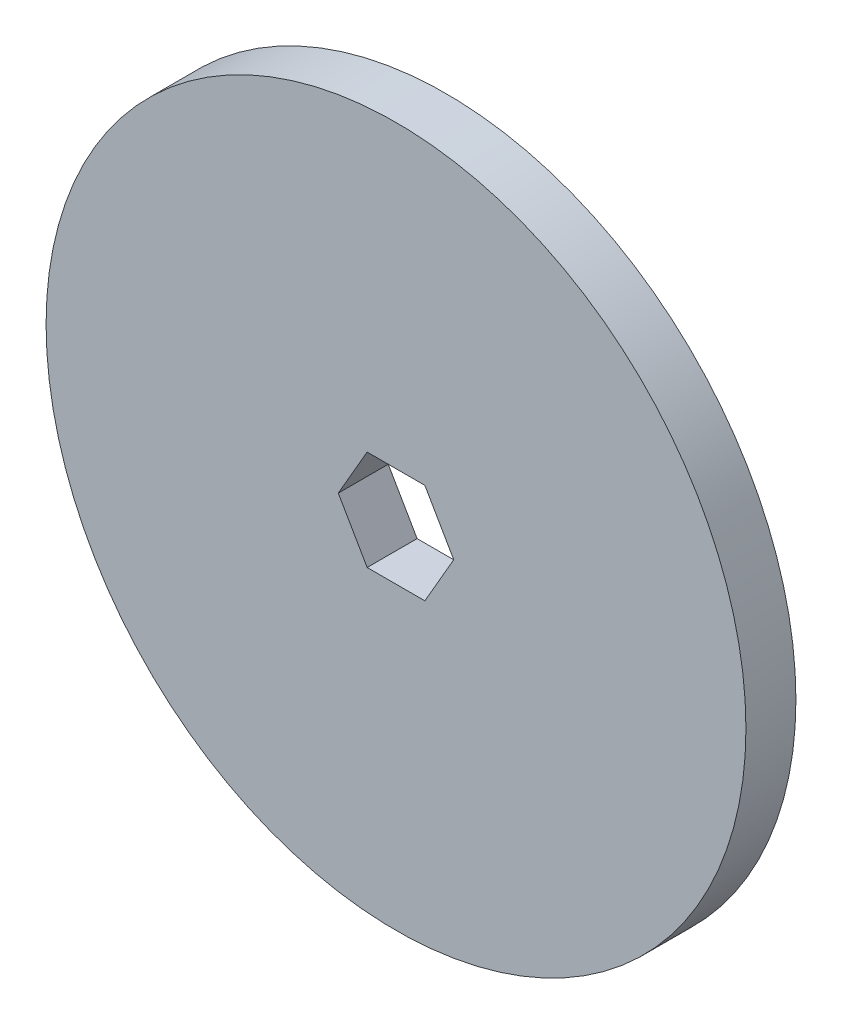
SolidWorks part; units mm, degrees
ref_plane "Front Plane" through (0, 0, 0) normal (0, 0, 1) x (1, 0, 0)
ref_plane "Top Plane" through (0, 0, 0) normal (0, 1, 0) x (1, 0, 0)
ref_plane "Right Plane" through (0, 0, 0) normal (1, 0, 0) x (0, 0, -1)
sketch "Sketch1" plane through (0, 0, 0) normal (0, 0, 1) x (1, 0, 0)
  circle A0 centre (0, 0) radius 44.45
  dimension "D1" = 88.9
extrude "Boss-Extrude1" add sketch "Sketch1" along normal mid plane 6.35
sketch "Sketch2" plane through (0, 0, 0) normal (0, 0, 1) x (1, 0, 0)
  line L1 (7.3323, 0) -> (3.6662, 6.35)
  line L2 (3.6662, 6.35) -> (-3.6662, 6.35)
  line L3 (-3.6662, 6.35) -> (-7.3323, 0)
  line L4 (-7.3323, 0) -> (-3.6662, -6.35)
  line L5 (-3.6662, -6.35) -> (3.6662, -6.35)
  line L6 (3.6662, -6.35) -> (7.3323, 0)
  circle A0 centre (0, 0) radius 6.35 construction
  dimension "D1" = 12.7
extrude "Cut-Extrude1" cut sketch "Sketch2" against normal mid plane 6.35
